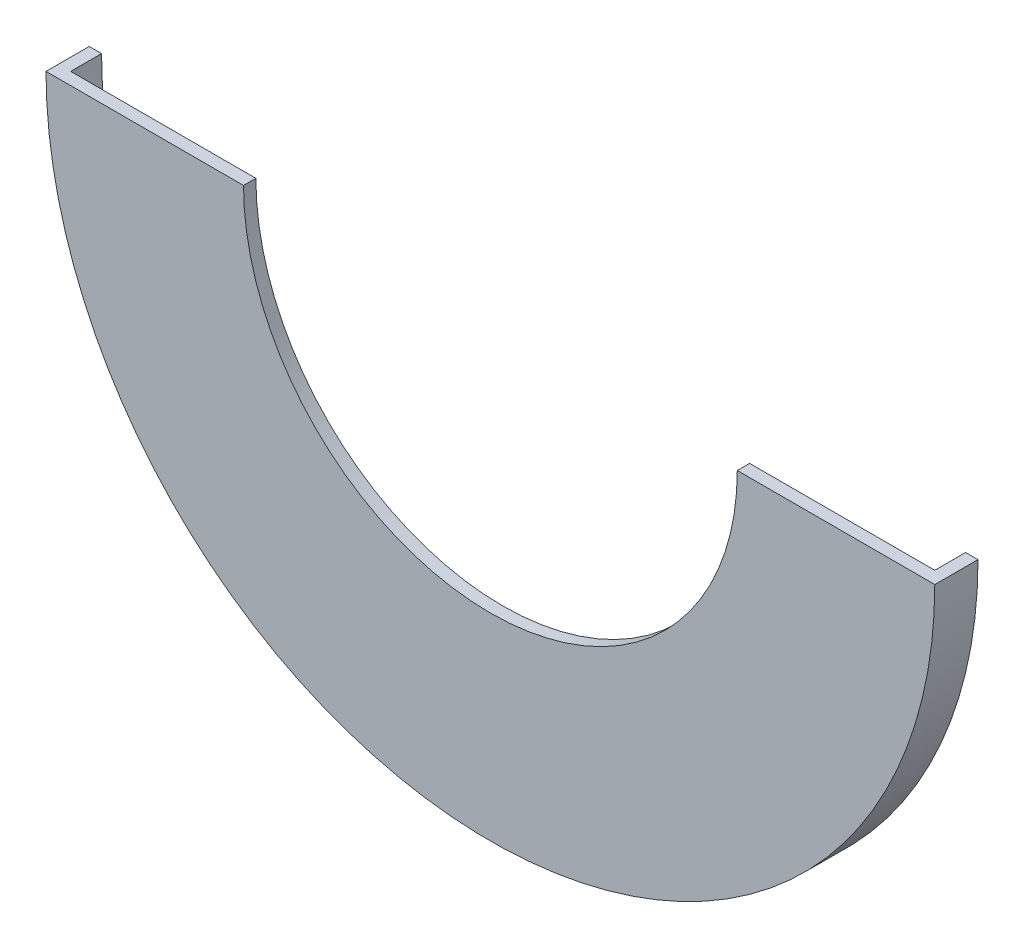
SolidWorks part; units mm, degrees
ref_plane "Front Plane" through (0, 0, 0) normal (0, 0, 1) x (1, 0, 0)
ref_plane "Top Plane" through (0, 0, 0) normal (0, 1, 0) x (1, 0, 0)
ref_plane "Right Plane" through (0, 0, 0) normal (1, 0, 0) x (0, 0, -1)
sketch "Sketch1" plane through (0, 0, 0) normal (0, 0, 1) x (1, 0, 0)
  line L0 (-72, 0) -> (72, 0)
  circle A0 centre (0, 0) radius 72
  circle A1 centre (0, 0) radius 70
  point P7 (0, 0)
extrude "Boss-Extrude1" add sketch "Sketch1" along normal blind 5 contours A1 L0 A0
sketch "Sketch2" plane through (0, 0, 5) normal (0, 0, 1) x (1, 0, 0)
  line L0 (-80, 0) -> (80, 0)
  circle A0 centre (0, 0) radius 80
  circle A1 centre (0, 0) radius 40
  point P7 (0, 0)
  arc M1 (70, 0) -> (-70, 0) centre (0, 0) cw
  line M2 (-70, 0) -> (-72, 0)
  arc M3 (-72, 0) -> (72, 0) centre (0, 0) ccw
  line M4 (72, 0) -> (70, 0)
extrude "Boss-Extrude2" add sketch "Sketch2" along normal blind 2 contours M4 M1 M2 M3 | A1 L0 M1
